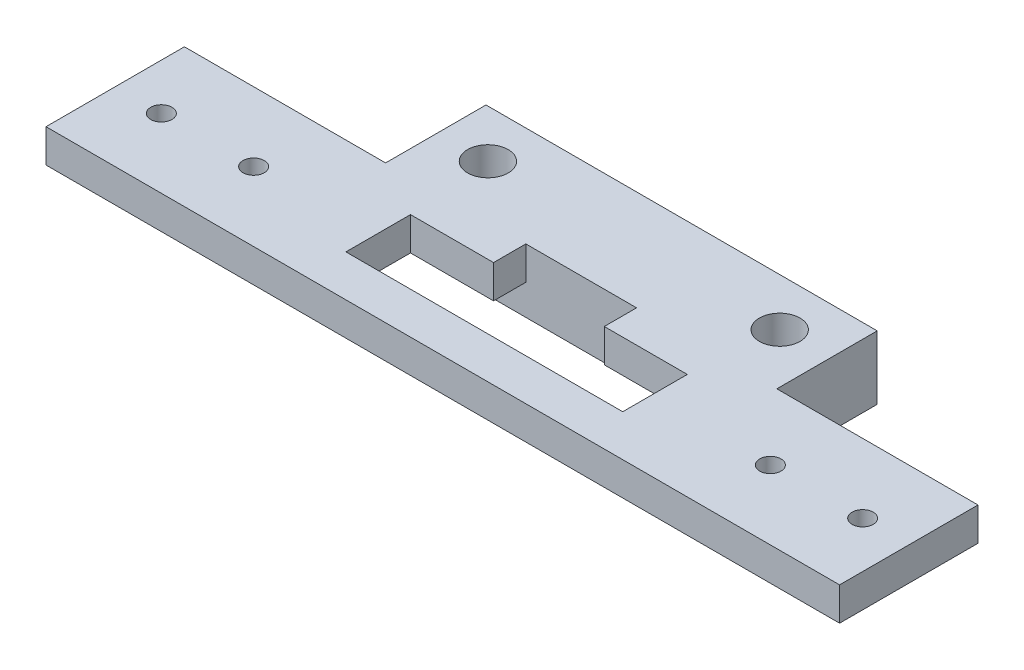
SolidWorks part; units mm, degrees
ref_plane "Front Plane" through (0, 0, 0) normal (0, 0, 1) x (1, 0, 0)
ref_plane "Top Plane" through (0, 0, 0) normal (0, 1, 0) x (1, 0, 0)
ref_plane "Right Plane" through (0, 0, 0) normal (1, 0, 0) x (0, 0, -1)
sketch "Sketch1" plane through (0, 0, 0) normal (0, 1, 0) x (1, 0, 0)
  line L0 (0, 0) -> (0, 7.5)
  line L1 (0, 7.5) -> (33, 7.5)
  line L2 (33, 7.5) -> (33, 0)
  line L3 (33, 0) -> (38, 0)
  line L4 (-33, 0) -> (-28, 0)
  line L5 (0, 7.5) -> (-33, 7.5)
  line L6 (-33, 7.5) -> (-33, 0)
  line L7 (33, 0) -> (28, 0)
  line L8 (-33, 7.5) -> (-43, 7.5)
  line L9 (-43, 7.5) -> (-43, -7.5)
  line L10 (-33, 0) -> (-38, 0)
  line L11 (-43, -7.5) -> (43, -7.5)
  line L12 (43, -7.5) -> (43, 7.5)
  line L13 (43, 7.5) -> (33, 7.5)
  line L14 (0, 7.5) -> (21.2, 7.5)
  line L15 (21.2, 7.5) -> (21.2, 13.2)
  line L16 (0, 7.5) -> (-21.2, 7.5)
  line L17 (-21.2, 7.5) -> (-21.2, 13.2)
  line L18 (0, 7.5) -> (0, 13.2)
  line L19 (0, 13.2) -> (15.81, 13.2)
  line L20 (0, 13.2) -> (-15.81, 13.2)
  line L21 (21.2, 13.2) -> (21.2, 18.38)
  line L22 (21.2, 18.38) -> (-21.2, 18.38)
  line L23 (-21.2, 18.38) -> (-21.2, 13.2)
  line L24 (0, 0) -> (-15, 0)
  line L25 (-15, 0) -> (-15, -3)
  line L26 (-15, -3) -> (15, -3)
  line L27 (15, -3) -> (15, 0)
  line L28 (15, 0) -> (15, 4)
  line L29 (15, 4) -> (-15, 4)
  line L30 (-15, 4) -> (-15, 0)
  line L31 (0, 4) -> (6, 4)
  line L33 (6, 4) -> (6, 7.5)
  line L35 (6, 7.5) -> (-6, 7.5)
  line L36 (-6, 7.5) -> (-6, 4)
  circle A0 centre (-38, 0) radius 1.15
  circle A1 centre (-28, 0) radius 1.15
  circle A2 centre (28, 0) radius 1.15
  circle A3 centre (38, 0) radius 1.15
  circle A4 centre (15.81, 13.2) radius 2.2
  circle A5 centre (-15.81, 13.2) radius 2.2
extrude "Boss-Extrude2" add sketch "Sketch1" along normal blind 3.6
sketch "Sketch2" plane through (0, 0, 0) normal (0, -1, 0) x (1, 0, 0)
  line L0 (21.2, -18.38) -> (21.2, -7.5)
  line L1 (21.2, -7.5) -> (21.2, -18.38) construction
  line L2 (21.2, -7.5) -> (-21.2, -7.5)
  line L3 (-21.2, -18.38) -> (-21.2, -7.5) construction
  line L4 (-21.2, -7.5) -> (-21.2, -18.38)
  line L5 (-21.2, -18.38) -> (21.2, -18.38)
  line L7 (-11.7685, -13.2) -> (-13.7893, -9.7)
  line L8 (-13.7893, -9.7) -> (-17.8307, -9.7)
  line L9 (-17.8307, -9.7) -> (-19.8515, -13.2)
  line L10 (-19.8515, -13.2) -> (-17.8307, -16.7)
  line L11 (-17.8307, -16.7) -> (-13.7893, -16.7)
  line L12 (-13.7893, -16.7) -> (-11.7685, -13.2)
  line L13 (19.8515, -13.2) -> (17.8307, -9.7)
  line L14 (17.8307, -9.7) -> (13.7893, -9.7)
  line L15 (13.7893, -9.7) -> (11.7685, -13.2)
  line L16 (11.7685, -13.2) -> (13.7893, -16.7)
  line L17 (13.7893, -16.7) -> (17.8307, -16.7)
  line L18 (17.8307, -16.7) -> (19.8515, -13.2)
  circle A0 centre (-15.81, -13.2) radius 3.5 construction
  circle A1 centre (15.81, -13.2) radius 3.5 construction
extrude "Boss-Extrude3" add sketch "Sketch2" along normal blind 3.3
